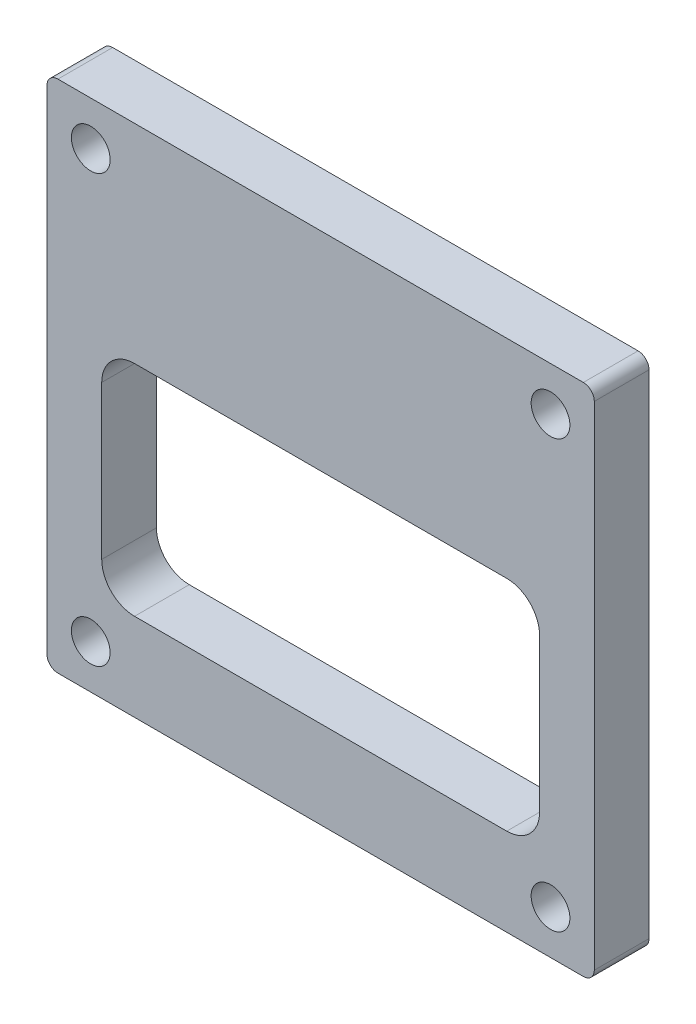
SolidWorks part; units mm, degrees
material "NEOPRENE"
ref_plane "Front Plane" through (0, 0, 0) normal (0, 0, 1) x (1, 0, 0)
ref_plane "Top Plane" through (0, 0, 0) normal (0, 1, 0) x (1, 0, 0)
ref_plane "Right Plane" through (0, 0, 0) normal (1, 0, 0) x (0, 0, -1)
sketch "Sketch1" plane through (0, 0, 0) normal (0, 0, 1) x (1, 0, 0)
  line L0 (6.35, 35.56) -> (6.35, 10.16) construction
  line L1 (0, 0) -> (63.5, 0)
  line L2 (0, 0) -> (0, 59.69)
  line L3 (0, 59.69) -> (63.5, 59.69)
  line L4 (63.5, 0) -> (63.5, 59.69)
  line L5 (6.35, 10.16) -> (57.15, 10.16) construction
  line L6 (57.15, 10.16) -> (57.15, 35.56) construction
  line L7 (57.15, 35.56) -> (6.35, 35.56) construction
  line L8 (31.75, 0) -> (31.75, 10.16) construction
  point P11 (5.08, 54.61)
  point P12 (58.42, 54.61)
  point P13 (58.42, 5.08)
  point P14 (5.08, 5.08)
  dimension "D1" = 5.08
  dimension "D2" = 5.08
  dimension "D3" = 25.4
  dimension "D4" = 50.8
  dimension "D5" = 5.08
  dimension "D6" = 5.08
  dimension "D7" = 5.08
  dimension "D8" = 19.05
  dimension "D9" = 6.35
extrude "Boss-Extrude1" add sketch "Sketch1" along normal blind 6.35
fillet "Fillet1" radius 1.27 4 edges at (0, 0, 3.175) (63.5, 0, 3.175) (63.5, 59.69, 3.175) (0, 59.69, 3.175)
sketch "Sketch6" plane through (0, 0, 6.35) normal (0, 0, 1) x (1, 0, 0)
  line L0 (31.75, 59.69) -> (31.75, 22.225) construction
  line L1 (6.35, 9.525) -> (57.15, 9.525) construction
  line L2 (6.35, 9.525) -> (6.35, 22.225) construction
  line L3 (6.35, 22.225) -> (57.15, 22.225) construction
  line L4 (57.15, 9.525) -> (57.15, 22.225) construction
  line L5 (62.23, 59.69) -> (1.27, 59.69) construction
  line L6 (1.27, 0) -> (62.23, 0) construction
  dimension "D1" = 50.8
  dimension "D2" = 12.7
  dimension "D3" = 9.525
hole_wizard "#8 Clearance Hole1" positions "Sketch5" profile "Sketch4" hole size "#8" standard "ANSI Inch" end condition through all
sketch "Sketch5" plane through (0, 0, 6.35) normal (0, 0, 1) x (1, 0, 0)
  line L5 (31.75, 59.69) -> (31.75, 0) construction
  line L6 (62.23, 59.69) -> (1.27, 59.69) construction
  line L7 (1.27, 0) -> (62.23, 0) construction
  line L10 (0, 29.845) -> (63.5, 29.845) construction
  line L11 (0, 58.42) -> (0, 1.27) construction
  line L12 (63.5, 1.27) -> (63.5, 58.42) construction
  point P78 (5.08, 54.61)
  point P81 (58.42, 54.61)
  point P84 (58.42, 5.08)
  point P87 (5.08, 5.08)
sketch "Sketch4" plane through (5.08, 54.61, 6.35) normal (1, 0, 0) x (0, -1, 0)
  line L0 (0, 0) -> (0, 6.35)
  line L1 (0, 6.35) -> (2.2479, 6.35)
  line L2 (2.2479, 6.35) -> (2.2479, 0)
  line L5 (2.2479, 0) -> (0, 0)
  line L11 (0, -6.35) -> (0, 107.95) construction
  dimension "Thru Hole Dia." = 4.4958
  dimension "Thru Hole Depth" = 6.35
sketch "Sketch7" plane through (0, 0, 6.35) normal (0, 0, 1) x (1, 0, 0)
  line L1 (6.35, 35.56) -> (57.15, 35.56)
  line L2 (6.35, 35.56) -> (6.35, 10.16)
  line L3 (6.35, 10.16) -> (57.15, 10.16)
  line L4 (57.15, 35.56) -> (57.15, 10.16)
extrude "Cut-Extrude1" cut sketch "Sketch7" against normal through all
fillet "Fillet2" radius 3.81 4 edges at (57.15, 35.56, 3.175) (57.15, 10.16, 3.175) (6.35, 10.16, 3.175) (6.35, 35.56, 3.175)
equation "\"pl\"=0.1"
